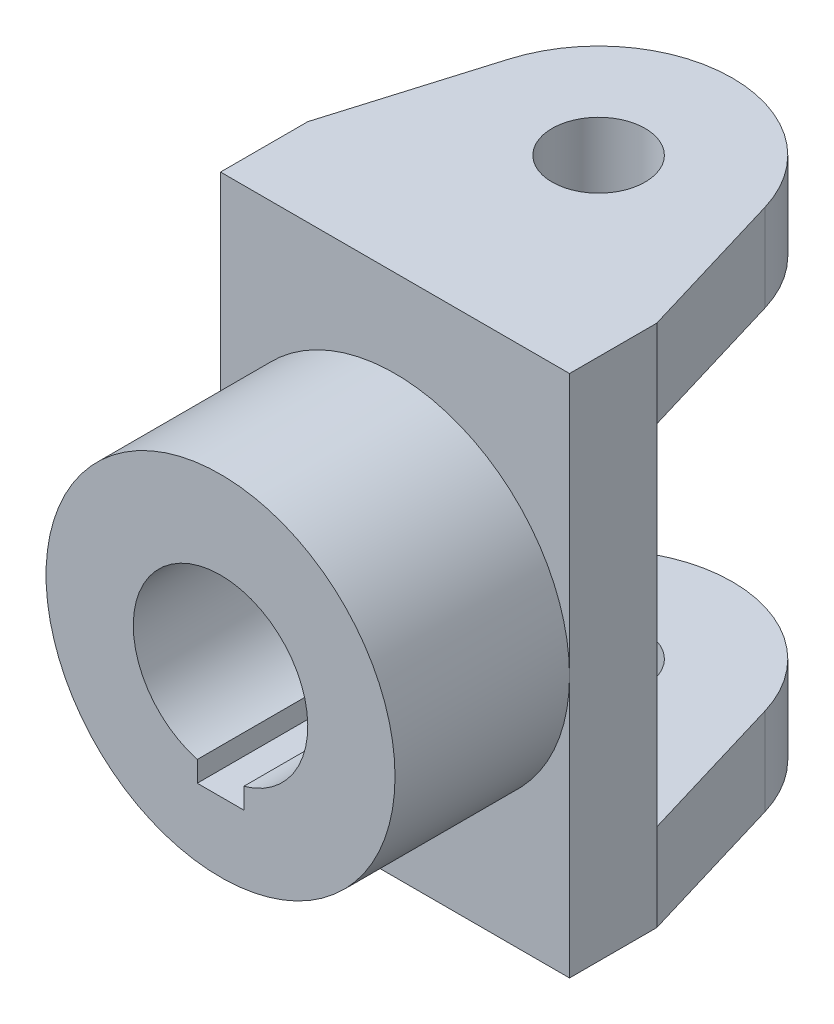
SolidWorks part; units mm, degrees
ref_plane "Front Plane" through (0, 0, 0) normal (0, 0, 1) x (1, 0, 0)
ref_plane "Top Plane" through (0, 0, 0) normal (0, 1, 0) x (1, 0, 0)
ref_plane "Right Plane" through (0, 0, 0) normal (1, 0, 0) x (0, 0, -1)
sketch "Sketch1" plane through (0, 0, 0) normal (0, 0, 1) x (1, 0, 0)
  line L1 (-30, 45) -> (30, 45)
  line L2 (-30, 45) -> (-30, -45)
  line L3 (-30, -45) -> (30, -45)
  line L4 (30, 45) -> (30, -45)
  line L5 (-30, 45) -> (30, -45) construction
  line L6 (-30, -45) -> (30, 45) construction
  point P0 (0, 0)
  dimension "D1" = 90
  dimension "D2" = 60
extrude "Boss-Extrude1" add sketch "Sketch1" along normal mid plane 15
sketch "Sketch2" plane through (0, 0, 7.5) normal (0, 0, 1) x (1, 0, 0)
  line L3 (0, -18) -> (4, -18)
  line L4 (4, -14.4568) -> (4, -18)
  line L5 (0, -15) -> (-4, -15)
  line L7 (0, -18) -> (-4, -18)
  line L8 (-4, -14.4568) -> (-4, -18)
  circle A0 centre (0, 0) radius 15
  circle A1 centre (0, 0) radius 30
  dimension "D1" = 30
  dimension "D2" = 60
  dimension "D3" = 4
  dimension "D4" = 4
  dimension "D5" = 3
extrude "Boss-Extrude4" add sketch "Sketch2" along normal blind 30 contours A1 A0 L4 L3 L7 L8
sketch "Sketch3" plane through (0, 45, 0) normal (0, 1, 0) x (1, 0, 0)
  line L0 (30, -7.5) -> (-30, -7.5) construction
  line L1 (-30, 7.5) -> (-22.0329, 34.0993)
  line L2 (-30, 7.5) -> (30, 7.5)
  line L3 (30, 7.5) -> (22.0329, 34.0993)
  circle A0 centre (0, 27.5) radius 8
  circle A1 centre (0, 27.5) radius 23
  point P5 (0, -7.5)
  line M3 (30, 7.5) -> (-30, 7.5)
  dimension "D1" = 46
  dimension "D2" = 16
  dimension "D3" = 35
extrude "Boss-Extrude5" add sketch "Sketch3" against normal blind 15 contours A1 L1 M3 | A1 L3 M3 | L2 A1 A0
mirror "Mirror1" about plane through (0, 0, 0) normal (0, 1, 0) of "Boss-Extrude5"
